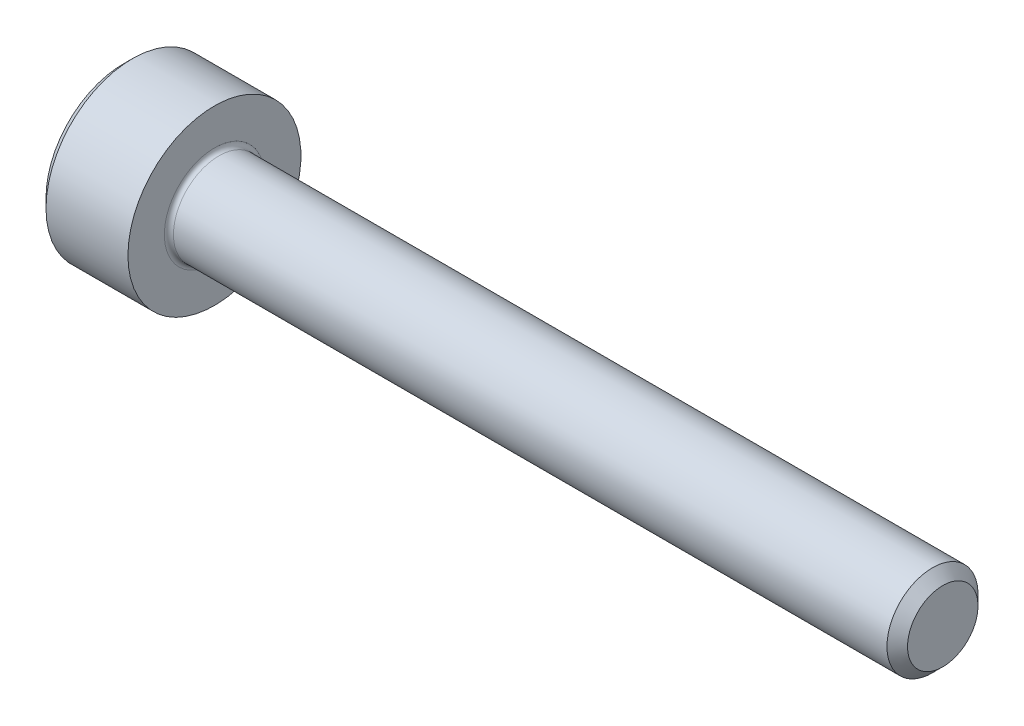
SolidWorks part; units mm, degrees
revolve "Base-Revolve" add sketch "BodySke"
sketch "BodySke" plane through (0, 0, 0) normal (0, 0, 1) x (1, 0, 0)
  line L0 (0, 0) -> (0, 1.7)
  line L1 (0.2, 1.9) -> (2, 1.9)
  line L2 (2, 1.9) -> (2, 1)
  line L3 (2, 1) -> (17.774, 1)
  line L4 (18, 0.774) -> (18, 0)
  line L5 (18, 0) -> (0, 0)
  line L6 (-31.75, 0) -> (127, 0) construction
  line L7 (0, 1.7) -> (0.2, 1.9)
  line L8 (18, 0.774) -> (17.774, 1)
  line L9 (0, -1.7) -> (0.2, -1.9) construction
  line L10 (18, -0.774) -> (17.774, -1) construction
  line L11 (2.4, 9.525) -> (2.4, 3.175) construction
  line L12 (2, 9.525) -> (2, 3.175) construction
  line L13 (-32, 9.525) -> (-32, 3.175) construction
  dimension "Diameter" = 2
  dimension "Head_ht" = 2
  dimension "Length" = 16
  dimension "Body_ch_ang" = 45
  dimension "Head_dia" = 3.8
  dimension "Head_ch_ang" = 45
  dimension "Minor_dia" = 1.548
  dimension "Advance" = 0.4
  dimension "Thread_nom" = 16
  dimension "Thread_length" = 50
  dimension "Head_ch_ht" = 0.2
cosmetic thread "ThreadCosmetic" [suppressed]
fillet "Fillet1" radius 0.1 1 edges at (2, 0, 1)
ref_plane "Plane1" through (0, 0, 0) normal (0, 0, 1) x (1, 0, 0)
ref_plane "Plane2" through (0, 0, 0) normal (0, 1, 0) x (1, 0, 0)
ref_plane "Plane3" through (0, 0, 0) normal (1, 0, 0) x (0, 0, -1)
sketch "Sketch2" plane through (0, 0, 0) normal (0, 0, 1) x (1, 0, 0)
  line L0 (0, 0.7725) -> (1, 0.7725)
  line L1 (1, 0.7725) -> (1.446, 0)
  line L2 (-31.75, 0) -> (127, 0) construction
  line L3 (1.446, 0) -> (0, 0)
  line L4 (0, 0) -> (0, 0.7725)
  line L5 (0, 1.7) -> (0, -1.7) construction
  line L6 (0, 0) -> (47.625, 0) construction
  line L7 (2, -1.9) -> (2, 1.9) construction
  dimension "D1" = 0.7725
  dimension "D2" = 60
revolve "Hex-PreBroach" cut sketch "Sketch2" angle 360 about L6
sketch "Sketch3" plane through (0, 0, 0) normal (-1, 0, 0) x (0, 0.5, 0.866)
  line L0 (0.446, 0.7725) -> (-0.446, 0.7725)
  line L1 (-0.446, 0.7725) -> (-0.892, 0)
  line L2 (0.446, 0.7725) -> (0.892, 0)
  line L3 (0.446, -0.7725) -> (0.892, 0)
  line L4 (0.446, -0.7725) -> (-0.446, -0.7725)
  line L5 (-0.446, -0.7725) -> (-0.892, 0)
  dimension "D1" = 0.7725
  dimension "D2" = 0.7725
  dimension "Hex_size" = 1.545
extrude "Hex" cut sketch "Sketch3" against normal blind 1
sketch "Sketch4" plane through (0, 0, 0) normal (-1, 0, 0) x (0, 0, 1)
  line L0 (0, 0) -> (0.9398, 0)
  line L1 (0, 0) -> (6.1484, 3.5498) construction
  line L2 (0, 0) -> (0.4699, 0.8139)
  line L3 (0.7832, 0.2175) -> (0.8962, 0.2828)
  line L4 (0.58, 0.5695) -> (0.693, 0.6348)
  arc A0 (0.7832, 0.2175) -> (0.58, 0.5695) centre (0, 0) ccw
  arc A1 (0.9398, 0) -> (0.8962, 0.2828) centre (0, 0) ccw
  arc A2 (0.4699, 0.8139) -> (0.693, 0.6348) centre (0, 0) cw
  dimension "D1" = 30
  dimension "D2" = 60
  dimension "Spline_p_dim" = 0.4064
  dimension "D3" = 0.2032
extrude "Spline" [suppressed] cut sketch "Sketch4" against normal blind 1
pattern_circular "CirPattern1" [suppressed] count 6 every 60
sketch "Sketch5" plane through (0, 0, 0) normal (0, 0, 1) x (1, 0, 0)
  line L0 (-31.75, 0) -> (127, 0) construction
  line L2 (0, 1.7) -> (0, -1.7) construction
  circle A0 centre (0.1, 0) radius 0.005
  dimension "Drilled_hole_dia" = 0.01
  dimension "Drilled_hole_loc" = 0.1
extrude "Hole" [suppressed] cut sketch "Sketch5" against normal through all and the other way through all
pattern_circular "Drilled-4" [suppressed] count 2 every 60
pattern_circular "Drilled-6" [suppressed] count 3 every 60
sketch "ThdSchSke" plane through (0, 0, 0) normal (0, 0, 1) x (1, 0, 0)
  line L0 (2.4, -0.774) -> (2.2418, -1)
  line L1 (2.4, -0.774) -> (2.5582, -1)
  line L2 (2.5582, -1) -> (2.5582, -1.25)
  line L3 (-3.175, 0) -> (5.1513, 0) construction
  line L5 (2.5582, -1.25) -> (2.2418, -1.25)
  line L6 (2.2418, -1.25) -> (2.2418, -1)
  line L7 (0, 1.7) -> (0, -1.7) construction
  dimension "Thread_minor" = 1.548
  dimension "Diameter" = 2
  dimension "Start" = 2.4
revolve "ThreadSchematic" [suppressed] cut sketch "ThdSchSke" angle 360 about L3
pattern_linear "ThdSchPat" [suppressed]
equation "\"D2@Sketch3\" = \"Hex_size@Sketch3\" / 2"
equation "\"D1@Sketch3\" = \"Hex_size@Sketch3\" / 2"
equation "\"D1@Sketch2\" = \"Hex_size@Sketch3\" / 2"
equation "\"D3@Sketch4\" = \"Spline_p_dim@Sketch4\" / 2"
equation "\"Thread_minor@ThreadCosmetic\"  =  \"Minor_dia@BodySke\""
equation "\"D2@CirPattern1\" = 360 / \"Num_teeth@CirPattern1\""
equation "\"Wall_thickness@Sketch2\" = \"Head_ht@BodySke\" - \"Key_eng@Hex\""
equation "\"Thread_length@ThreadCosmetic\" = ((sgn( (\"Length@BodySke\" - \"Advance@BodySke\" ) - \"Thread_nom@BodySke\" )-1)*( (\"Length@BodySke\" - \"Advance@BodySke\" ) - \"Thread_nom@BodySke\" ))/-2+ \"Thread_nom@BodySke\""
equation "\"Thread_minor@ThdSchSke\" = \"Minor_dia@BodySke\""
equation "\"Diameter@ThdSchSke\" = \"Diameter@BodySke\""
equation "\"Overcut@ThdSchSke\" = \"Diameter@BodySke\" * 1.25"
equation "\"Start@ThdSchSke\" = \"Head_ht@BodySke\" + \"Length@BodySke\" - \"Thread_length@ThreadCosmetic\"  '---Non-countersunk---"
equation "\"Num_threads@ThdSchPat\" = int( \"Thread_length@ThreadCosmetic\" / \"Advance@BodySke\" + 0.999 )  + 1"
equation "\"Advance@ThdSchPat\" = \"Thread_length@ThreadCosmetic\" /  (\"Num_threads@ThdSchPat\" - 1) 'relax it"
equation "\"Num_threads@ThdSchPat\" = \"Num_threads@ThdSchPat\" - sgn( \"Num_threads@ThdSchPat\" - 1) '---chamfered tips only---"
